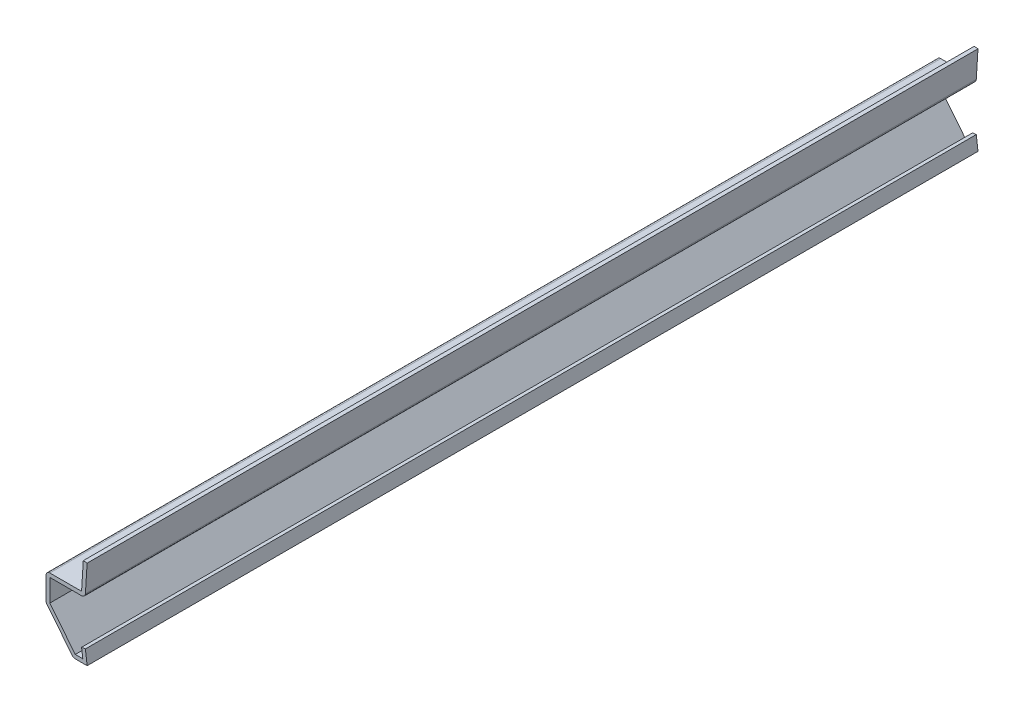
SolidWorks part; units mm, degrees
ref_plane "Front Plane" through (0, 0, 0) normal (0, 0, 1) x (1, 0, 0)
ref_plane "Top Plane" through (0, 0, 0) normal (0, 1, 0) x (1, 0, 0)
ref_plane "Right Plane" through (0, 0, 0) normal (1, 0, 0) x (0, 0, -1)
sketch "Sketch1" plane through (0, 0, 0) normal (0, 0, 1) x (1, 0, 0)
  line L0 (-0.3969, 3.175) -> (0, 0)
  line L1 (0, 0) -> (-3.175, 0)
  line L2 (-3.175, 0) -> (-9.525, 7.9375)
  line L3 (-9.525, 7.9375) -> (-9.525, 14.2875)
  line L4 (-9.525, 14.2875) -> (-1.2859, 14.2875)
  line L5 (-1.2859, 14.2875) -> (-0.889, 20.6375)
  line L6 (0, 20.6375) -> (0, 0) construction
  point P3 (0, 0)
extrude "Extrude-Thin1" add sketch "Sketch1" against normal blind 206.375 thin
fillet "Fillet1" radius 0.889 4 edges at (-3.175, 0, -103.1875) (-9.525, 7.9375, -103.1875) (-0.4507, 13.3985, -103.1875) (-9.525, 14.2875, -103.1875)
equation "\"D1@Extrude-Thin1\"=\"D10@Sketch1\"*10"
